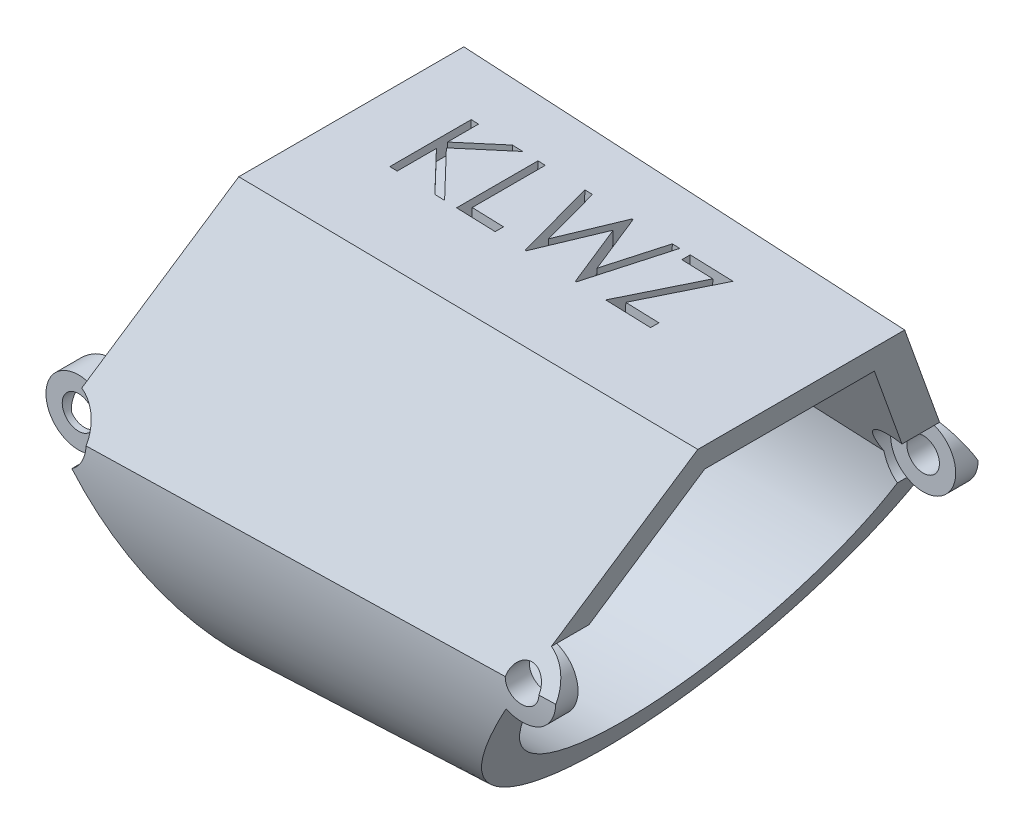
SolidWorks part; units mm, degrees
material "1060 Alloy"
ref_plane "Front Plane" through (0, 0, 0) normal (0, 0, 1) x (1, 0, 0)
ref_plane "Top Plane" through (0, 0, 0) normal (0, 1, 0) x (1, 0, 0)
ref_plane "Right Plane" through (0, 0, 0) normal (1, 0, 0) x (0, 0, -1)
sketch "Sketch1" plane through (0, 0, 0) normal (1, 0, 0) x (0, 0, -1)
  line L0 (-4.445, 0) -> (4.445, 0)
  line L1 (4.445, 0) -> (8.89, -7.699)
  line L2 (-4.445, 0) -> (-8.89, -7.699)
  arc A0 (-8.89, -7.699) -> (8.89, -7.699) centre (0, -8.207) ccw
  point P6 (0, 0)
  dimension "D4" = 0.508
  dimension "D1" = 8.89
  dimension "D2" = 120
  dimension "D3" = 120
extrude "Boss-Extrude1" add sketch "Sketch1" along normal blind 20.32 draft 2
shell "Shell1" thickness 1.27
sketch "Sketch4" plane through (0, 0, 0) normal (-1, 0, 0) x (0, 0, 1)
  line L0 (-7.5956, -8.969) -> (-7.874, -8.969)
  line L1 (-7.874, -8.969) -> (-7.874, -6.429)
  line L2 (-7.874, -6.429) -> (-6.6894, -6.429)
  line L3 (-7.6324, -8.0622) -> (-3.7113, -1.2708) construction
  line L4 (-6.6894, -6.429) -> (-7.6324, -8.0622)
  line L5 (0, -5.039) -> (0, -11.6807) construction
  line L6 (6.6894, -6.429) -> (7.6324, -8.0622)
  line L7 (7.874, -6.429) -> (6.6894, -6.429)
  line L8 (7.874, -8.969) -> (7.874, -6.429)
  line L9 (7.5956, -8.969) -> (7.874, -8.969)
  arc A0 (-7.6324, -8.0622) -> (7.6324, -8.0622) centre (0, -8.207) ccw construction
  arc A1 (-7.6324, -8.0622) -> (-7.5956, -8.969) centre (0, -8.207) ccw
  arc A2 (7.6324, -8.0622) -> (7.5956, -8.969) centre (0, -8.207) cw
  point P15 (-7.874, -7.699)
  dimension "D1" = 7.874
  dimension "D2" = 2.54
extrude "Boss-Extrude2" add sketch "Sketch4" along normal blind 1.27
sketch "Sketch2" plane through (0, 0, 0) normal (0, 0, 1) x (1, 0, 0)
  line L2 (0, -17.1115) -> (20.32, -16.4019) construction
  line L5 (20.32, -0.7096) -> (18.1451, -6.6851)
  line L7 (12.6348, -16.6703) -> (20.32, -16.4019)
  line L8 (20.32, -16.4019) -> (20.32, -0.7096)
  line L9 (0.7284, -8.7393) -> (6.8524, -17.4852)
  line L15 (-2.1296, -17.4852) -> (-2.1296, 2.0873)
  line L16 (-2.1296, 2.0873) -> (3.5619, 2.0873)
  line L17 (3.5619, 2.0873) -> (0.4344, -6.5056)
  line L19 (6.8524, -17.4852) -> (-2.1296, -17.4852)
  line L20 (17.0757, -8.9784) -> (12.6348, -16.6703)
  arc A0 (18.1451, -6.6851) -> (17.0757, -8.9784) centre (17.7107, -7.8785) cw
  arc A1 (0.4344, -6.5056) -> (0.7284, -8.7393) centre (0, -7.699) ccw
  circle A2 centre (0, -7.699) radius 0.635
  circle A3 centre (17.7107, -7.8785) radius 0.635
  spline S0 degree 3 poles (20.32, -7.9046) (13.5467, -7.8371) (6.7733, -7.7686) (0, -7.699) knots 0 0 0 0 0.020333 0.020333 0.020333 0.020333 construction
  point P9 (-2.1296, -7.699)
  dimension "D5" = 1.27
  dimension "D6" = 1.27
  dimension "D1" = 20
  dimension "D2" = 55
  dimension "D3" = 20
extrude "Cut-Extrude1" cut sketch "Sketch2" against normal through all both and the other way through all
ref_plane "Plane1" through (0, 0, 7.874) normal (0, 0, 1) x (1, 0, 0)
sketch "Sketch5" plane through (0, 0, 7.874) normal (0, 0, 1) x (1, 0, 0)
  circle A0 centre (0, -7.699) radius 1.27
extrude "Cut-Extrude3" cut sketch "Sketch5" along normal blind 1.27
mirror "Mirror1" about plane through (0, 0, 0) normal (0, 0, 1) of "Cut-Extrude3"
sketch "Sketch6" plane through (0, 0, 0) normal (0, 0, 1) x (1, 0, 0)
  circle A0 centre (17.7107, -7.8785) radius 1.27
extrude "Cut-Extrude4" cut sketch "Sketch6" against normal blind 7.366 and the other way blind 7.366
sketch "Sketch3" plane through (0, 0, 0) normal (0.0349, 0.9994, 0) x (0.9994, -0.0349, 0)
  text T0 "KLWZ" font "Century Gothic" height in points 12
extrude "Cut-Extrude2" cut sketch "Sketch3" against normal blind 0.762
